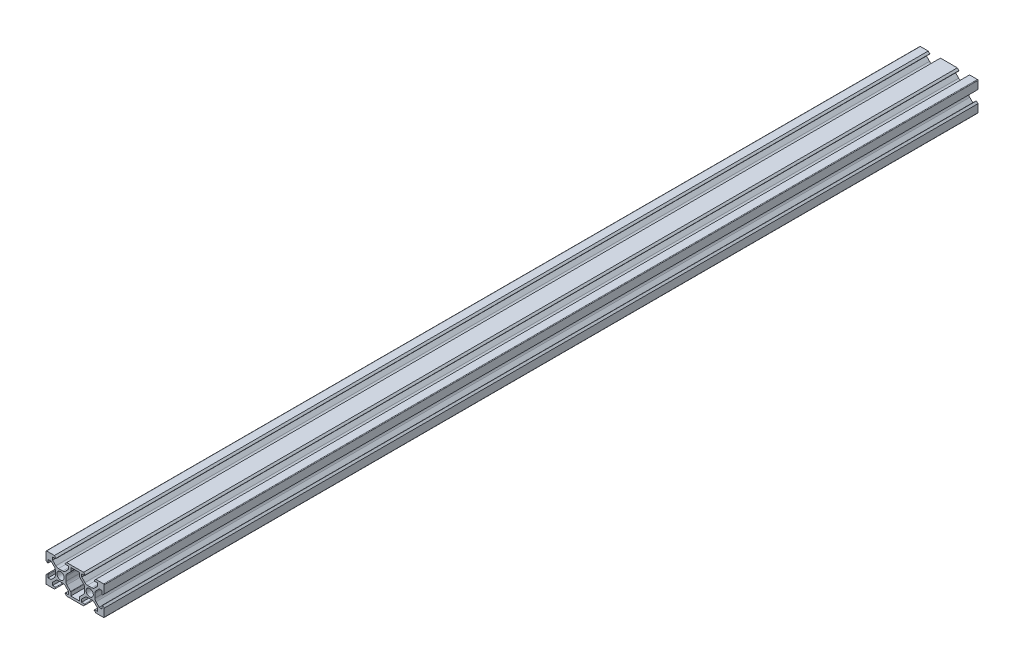
SolidWorks part; units mm, degrees
material "6063-T5"
ref_plane "Plano frontal" through (0, 0, 0) normal (0, 0, 1) x (1, 0, 0)
ref_plane "Plano superior" through (0, 0, 0) normal (0, 1, 0) x (1, 0, 0)
ref_plane "Plano direito" through (0, 0, 0) normal (1, 0, 0) x (0, 0, -1)
sketch "Esboço1" plane through (0, 0, 0) normal (0, 0, 1) x (1, 0, 0)
  line L0 (-13.1, 8.9) -> (-14.2, 10)
  line L1 (-19.6, 10) -> (-14.2, 10)
  line L2 (-13.6, 1.5038) -> (-13.6, 0)
  line L3 (-18.5, 5.5) -> (-18.5, 3.5)
  line L4 (-16.5607, 5.5) -> (-14.3322, 3.2716)
  line L5 (-18.5, 5.5) -> (-16.5607, 5.5)
  line L6 (-20, 9.6) -> (-20, 4.2)
  line L7 (-18.9, 3.1) -> (-20, 4.2)
  line L8 (-3, 8.5) -> (3, 8.5)
  line L9 (-3.1172, 5.8222) -> (-5.6678, 3.2716)
  line L10 (-8.4962, 3.6) -> (-10, 3.6)
  line L11 (-8.2322, 1.7678) -> (-10, 0) construction
  line L12 (-4.5, 6.5607) -> (-6.7284, 4.3322)
  line L13 (-15.5, 8.5) -> (-15.5, 6.5607)
  line L14 (-4.5, 8.5) -> (-4.5, 6.5607)
  line L15 (0, 0) -> (0, 8.5) construction
  line L16 (-6.9, 8.9) -> (-5.8, 10)
  line L17 (-6.4, 0) -> (6.4, 0) construction
  line L18 (-3, -8.5) -> (-3, -6.105)
  line L19 (-18.5, 8.5) -> (-18.5, -8.5) construction
  line L20 (-3.1172, -5.8222) -> (-5.6678, -3.2716)
  line L21 (-6.4, 1.5038) -> (-6.4, 0)
  line L22 (-5.8, -10) -> (5.8, -10)
  line L23 (-19.8828, 9.8828) -> (-10, 0) construction
  line L24 (-6.9, -8.9) -> (-5.8, -10)
  line L25 (-15.5, 6.5607) -> (-13.2716, 4.3322)
  line L26 (-3, -8.5) -> (3, -8.5)
  line L27 (-20, 10) -> (-20, -10) construction
  line L28 (-6.4, -1.5038) -> (-6.4, 0)
  line L29 (19.8828, -9.8828) -> (10, 0) construction
  line L30 (8.2322, -1.7678) -> (10, 0) construction
  line L31 (19.8828, 9.8828) -> (10, 0) construction
  line L32 (8.2322, 1.7678) -> (10, 0) construction
  line L33 (-15.5, 8.5) -> (-13.5, 8.5)
  line L34 (6.5, 8.5) -> (4.5, 8.5)
  line L35 (-4.5, -8.5) -> (-4.5, -6.5607)
  line L36 (-20, 10) -> (0, 10) construction
  line L37 (-4.5, -6.5607) -> (-6.7284, -4.3322)
  line L38 (-4.5, -8.5) -> (-6.5, -8.5)
  line L39 (-18.5, 8.5) -> (-1.5, 8.5) construction
  line L40 (-11.5038, 3.6) -> (-10, 3.6)
  line L41 (-8.4962, -3.6) -> (-10, -3.6)
  line L42 (-8.2322, -1.7678) -> (-10, 0) construction
  line L43 (-18.9, -3.1) -> (-20, -4.2)
  line L44 (-20, -9.6) -> (-20, -4.2)
  line L45 (-11.5038, -3.6) -> (-10, -3.6)
  line L46 (-15.5, -8.5) -> (-13.5, -8.5)
  line L47 (-15.5, -6.5607) -> (-13.2716, -4.3322)
  line L48 (-15.5, -8.5) -> (-15.5, -6.5607)
  line L49 (-19.6, -10) -> (-14.2, -10)
  line L50 (-13.1, -8.9) -> (-14.2, -10)
  line L51 (-18.5, -5.5) -> (-16.5607, -5.5)
  line L52 (-16.5607, -5.5) -> (-14.3322, -3.2716)
  line L53 (-18.5, -5.5) -> (-18.5, -3.5)
  line L54 (0, 10) -> (0, -10) construction
  line L55 (-20, -10) -> (0, -10) construction
  line L56 (-13.6, -1.5038) -> (-13.6, 0)
  line L57 (-18.5, -8.5) -> (-1.5, -8.5) construction
  line L58 (-1.5, 8.5) -> (-1.5, -8.5) construction
  line L59 (-19.8828, -9.8828) -> (-10, 0) construction
  line L60 (3, 8.5) -> (3, 6.105)
  line L61 (-3, 8.5) -> (-3, 6.105)
  line L62 (-6.5, 8.5) -> (-4.5, 8.5)
  line L63 (-5.8, 10) -> (5.8, 10)
  line L64 (13.6, -1.5038) -> (13.6, 0)
  line L65 (18.5, -5.5) -> (18.5, -3.5)
  line L66 (16.5607, -5.5) -> (14.3322, -3.2716)
  line L67 (18.5, -5.5) -> (16.5607, -5.5)
  line L68 (13.1, -8.9) -> (14.2, -10)
  line L69 (19.6, -10) -> (14.2, -10)
  line L70 (15.5, -8.5) -> (15.5, -6.5607)
  line L71 (15.5, -6.5607) -> (13.2716, -4.3322)
  line L72 (15.5, -8.5) -> (13.5, -8.5)
  line L73 (11.5038, -3.6) -> (10, -3.6)
  line L74 (20, -9.6) -> (20, -4.2)
  line L75 (18.9, -3.1) -> (20, -4.2)
  line L76 (8.4962, -3.6) -> (10, -3.6)
  line L77 (11.5038, 3.6) -> (10, 3.6)
  line L78 (4.5, -8.5) -> (6.5, -8.5)
  line L79 (4.5, -6.5607) -> (6.7284, -4.3322)
  line L80 (4.5, -8.5) -> (4.5, -6.5607)
  line L81 (15.5, 8.5) -> (13.5, 8.5)
  line L82 (6.4, -1.5038) -> (6.4, 0)
  line L83 (15.5, 6.5607) -> (13.2716, 4.3322)
  line L84 (6.9, -8.9) -> (5.8, -10)
  line L85 (6.4, 1.5038) -> (6.4, 0)
  line L86 (3.1172, -5.8222) -> (5.6678, -3.2716)
  line L87 (3, -8.5) -> (3, -6.105)
  line L88 (6.9, 8.9) -> (5.8, 10)
  line L89 (4.5, 8.5) -> (4.5, 6.5607)
  line L90 (15.5, 8.5) -> (15.5, 6.5607)
  line L91 (4.5, 6.5607) -> (6.7284, 4.3322)
  line L92 (8.4962, 3.6) -> (10, 3.6)
  line L93 (3.1172, 5.8222) -> (5.6678, 3.2716)
  line L94 (18.9, 3.1) -> (20, 4.2)
  line L95 (20, 9.6) -> (20, 4.2)
  line L96 (18.5, 5.5) -> (16.5607, 5.5)
  line L97 (16.5607, 5.5) -> (14.3322, 3.2716)
  line L98 (18.5, 5.5) -> (18.5, 3.5)
  line L99 (13.6, 1.5038) -> (13.6, 0)
  line L100 (19.6, 10) -> (14.2, 10)
  line L101 (13.1, 8.9) -> (14.2, 10)
  arc A0 (-10, 2.5) -> (-12.5, 0) centre (-10, 0) ccw
  arc A1 (-13.5, 8.5) -> (-13.1, 8.9) centre (-13.5, 8.9) ccw
  arc A2 (-19.6, 10) -> (-20, 9.6) centre (-19.6, 9.6) ccw
  arc A3 (-13.2716, 4.3322) -> (-11.5038, 3.6) centre (-11.5038, 6.1) ccw
  arc A4 (-14.3322, 3.2716) -> (-13.6, 1.5038) centre (-16.1, 1.5038) cw
  arc A5 (-18.5, 3.5) -> (-18.9, 3.1) centre (-18.9, 3.5) cw
  arc A6 (-7.5, 0) -> (-10, 2.5) centre (-10, 0) ccw
  arc A7 (-3, -6.105) -> (-3.1172, -5.8222) centre (-3.4, -6.105) ccw
  arc A8 (-3.1172, 5.8222) -> (-3, 6.105) centre (-3.4, 6.105) ccw
  arc A9 (-5.6678, 3.2716) -> (-6.4, 1.5038) centre (-3.9, 1.5038) ccw
  arc A10 (-6.7284, 4.3322) -> (-8.4962, 3.6) centre (-8.4962, 6.1) cw
  arc A11 (-6.5, 8.5) -> (-6.9, 8.9) centre (-6.5, 8.9) cw
  arc A12 (-10, -2.5) -> (-7.5, 0) centre (-10, 0) ccw
  arc A13 (-6.5, -8.5) -> (-6.9, -8.9) centre (-6.5, -8.9) ccw
  arc A14 (13.5, -8.5) -> (13.1, -8.9) centre (13.5, -8.9) ccw
  arc A15 (-6.7284, -4.3322) -> (-8.4962, -3.6) centre (-8.4962, -6.1) ccw
  arc A16 (-5.6678, -3.2716) -> (-6.4, -1.5038) centre (-3.9, -1.5038) cw
  arc A17 (13.2716, -4.3322) -> (11.5038, -3.6) centre (11.5038, -6.1) ccw
  arc A18 (-12.5, 0) -> (-10, -2.5) centre (-10, 0) ccw
  arc A19 (-18.5, -3.5) -> (-18.9, -3.1) centre (-18.9, -3.5) ccw
  arc A20 (-20, -9.6) -> (-19.6, -10) centre (-19.6, -9.6) ccw
  arc A21 (-14.3322, -3.2716) -> (-13.6, -1.5038) centre (-16.1, -1.5038) ccw
  arc A22 (-13.2716, -4.3322) -> (-11.5038, -3.6) centre (-11.5038, -6.1) cw
  arc A23 (-13.5, -8.5) -> (-13.1, -8.9) centre (-13.5, -8.9) cw
  arc A24 (14.3322, -3.2716) -> (13.6, -1.5038) centre (16.1, -1.5038) cw
  arc A25 (20, -9.6) -> (19.6, -10) centre (19.6, -9.6) cw
  arc A26 (18.5, -3.5) -> (18.9, -3.1) centre (18.9, -3.5) cw
  arc A27 (12.5, 0) -> (10, -2.5) centre (10, 0) cw
  arc A28 (5.6678, -3.2716) -> (6.4, -1.5038) centre (3.9, -1.5038) ccw
  arc A29 (6.7284, -4.3322) -> (8.4962, -3.6) centre (8.4962, -6.1) cw
  arc A30 (6.5, -8.5) -> (6.9, -8.9) centre (6.5, -8.9) cw
  arc A31 (10, -2.5) -> (7.5, 0) centre (10, 0) cw
  arc A32 (6.5, 8.5) -> (6.9, 8.9) centre (6.5, 8.9) ccw
  arc A33 (6.7284, 4.3322) -> (8.4962, 3.6) centre (8.4962, 6.1) ccw
  arc A34 (5.6678, 3.2716) -> (6.4, 1.5038) centre (3.9, 1.5038) cw
  arc A35 (3.1172, 5.8222) -> (3, 6.105) centre (3.4, 6.105) cw
  arc A36 (3, -6.105) -> (3.1172, -5.8222) centre (3.4, -6.105) cw
  arc A37 (7.5, 0) -> (10, 2.5) centre (10, 0) cw
  arc A38 (18.5, 3.5) -> (18.9, 3.1) centre (18.9, 3.5) ccw
  arc A39 (14.3322, 3.2716) -> (13.6, 1.5038) centre (16.1, 1.5038) ccw
  arc A40 (13.2716, 4.3322) -> (11.5038, 3.6) centre (11.5038, 6.1) cw
  arc A41 (19.6, 10) -> (20, 9.6) centre (19.6, 9.6) cw
  arc A42 (13.5, 8.5) -> (13.1, 8.9) centre (13.5, 8.9) cw
  arc A43 (10, 2.5) -> (12.5, 0) centre (10, 0) cw
  point P116 (-10, 0)
  point P168 (0, 10)
  point P183 (0, -8.5)
  point P185 (0, -10)
  dimension "D4" = 2.5
  dimension "D1" = 0.4
  dimension "D3" = 0.4
  dimension "D5" = 0.4
  dimension "D2" = 45
extrude "Ressalto-extrusão1" add sketch "Esboço1" along normal mid plane 600
